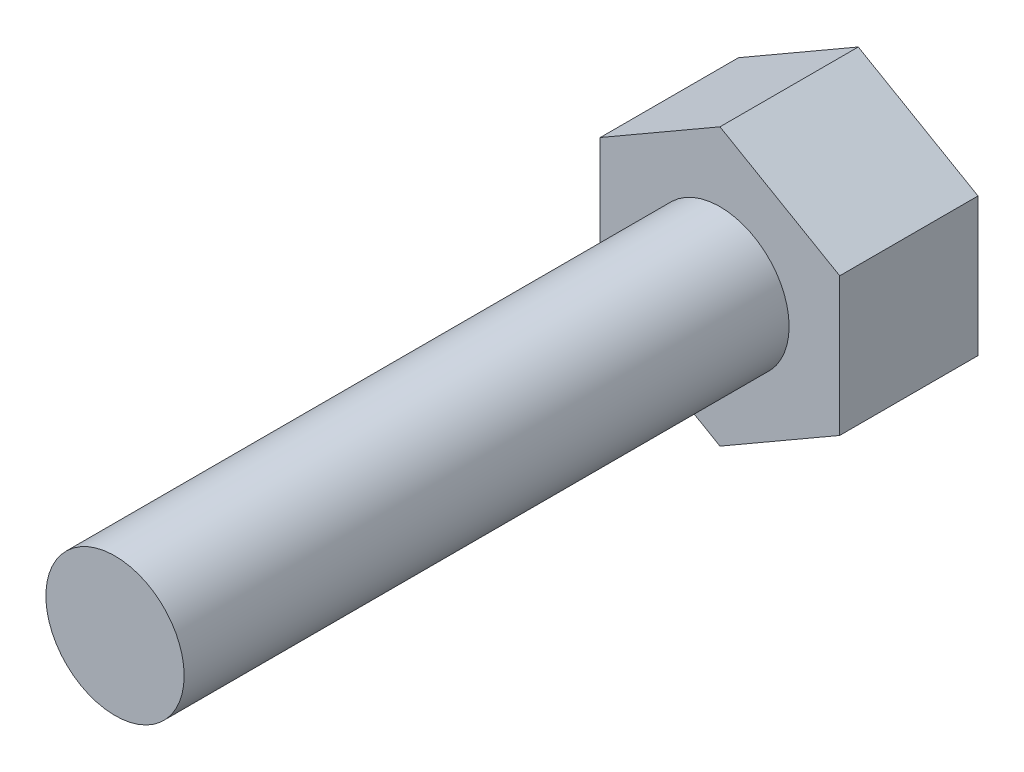
SolidWorks part; units mm, degrees
ref_plane "Front Plane" through (0, 0, 0) normal (0, 0, 1) x (1, 0, 0)
ref_plane "Top Plane" through (0, 0, 0) normal (0, 1, 0) x (1, 0, 0)
ref_plane "Right Plane" through (0, 0, 0) normal (1, 0, 0) x (0, 0, -1)
sketch "Sketch1" plane through (0, 0, 0) normal (0, 0, 1) x (1, 0, 0)
  line L1 (0, 24) -> (-20.7846, 12)
  line L2 (-20.7846, 12) -> (-20.7846, -12)
  line L3 (-20.7846, -12) -> (0, -24)
  line L4 (0, -24) -> (20.7846, -12)
  line L5 (20.7846, -12) -> (20.7846, 12)
  line L6 (20.7846, 12) -> (0, 24)
  circle A0 centre (0, 0) radius 20.7846 construction
  dimension "D1" = 48
extrude "Boss-Extrude2" add sketch "Sketch1" along normal blind 24
sketch "Sketch3" plane through (0, 0, 24) normal (0, 0, 1) x (1, 0, 0)
  circle A0 centre (0, 0) radius 12
  dimension "D1" = 24
extrude "Boss-Extrude3" add sketch "Sketch3" along normal blind 105
sketch "Sketch4" plane through (0, 0, 0) normal (1, 0, 0) x (0, 0, -1)
  line L0 (-129, 0) -> (-129, -12)
  line L1 (-129, 12) -> (-129, -12) construction
  line L2 (-129, 0) -> (-135.1649, 0)
  arc A0 (-129.0387, -11.9722) -> (-129, -12) centre (-120.4035, 0) ccw
  arc A1 (-129, -11.9524) -> (-135.1649, 0) centre (-132.0825, -5.9762) cw
